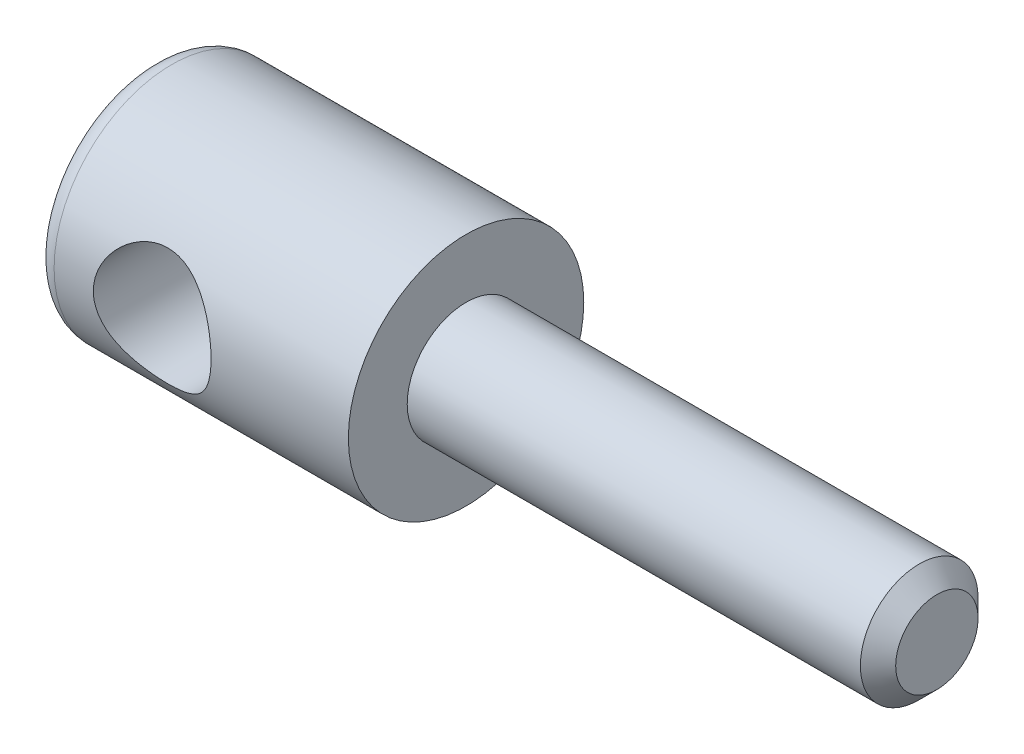
SolidWorks part; units mm, degrees
ref_plane "Front" through (0, 0, 0) normal (0, 0, 1) x (1, 0, 0)
ref_plane "Top" through (0, 0, 0) normal (0, 1, 0) x (1, 0, 0)
ref_plane "Right" through (0, 0, 0) normal (1, 0, 0) x (0, 0, -1)
sketch "Sketch1" plane through (0, 0, 0) normal (0, 0, 1) x (1, 0, 0)
  line L0 (0, 0) -> (72.7483, 0) construction
  line L1 (0, 0) -> (0, 9.525)
  line L2 (0, 9.525) -> (25.4, 9.525)
  line L3 (25.4, 9.525) -> (25.4, 4.7625)
  line L4 (25.4, 4.7625) -> (63.5, 4.7625)
  line L5 (63.5, 4.7625) -> (63.5, 0)
  line L6 (0, 0) -> (63.5, 0)
  dimension "D1" = 63.5
  dimension "D2" = 25.4
  dimension "D3" = 19.05
  dimension "D4" = 9.525
revolve "Revolve1" add sketch "Sketch1" angle 360 about L0
cosmetic thread "Cosmetic Thread1" parameters "D1"=25.4, "D2"=7.6327
ref_plane "Plane2" through (0, 0, 9.525) normal (0, 0, 1) x (1, 0, 0)
hole_wizard "3/8 (0.3750) Dowel Hole1" positions "Sketch3" profile "Sketch4" hole size "3/8" standard "ANSI Inch" end condition through all
sketch "Sketch3" plane through (0, 0, 9.525) normal (0, 0, 1) x (1, 0, 0)
  line L4 (0, 0) -> (13.7369, 0) construction
  point P0 (9.525, 0)
  dimension "D1" = 9.525
sketch "Sketch4" plane through (9.525, 0, 9.525) normal (1, 0, 0) x (0, -1, 0)
  line L0 (0, 0) -> (0, 19.05)
  line L1 (0, 19.05) -> (4.7625, 19.05)
  line L2 (4.7625, 19.05) -> (4.7625, 0)
  line L5 (4.7625, 0) -> (0, 0)
  line L11 (0, -6.35) -> (0, 107.95) construction
  dimension "Thru Hole Dia." = 9.525
  dimension "Thru Hole Depth" = 19.05
fillet "Fillet2" radius 1.5875 1 edges at (0, 0, 9.525)
chamfer "Chamfer3" distance 1.4287 angle 45 1 edges at (63.5, 0, 4.7625)
